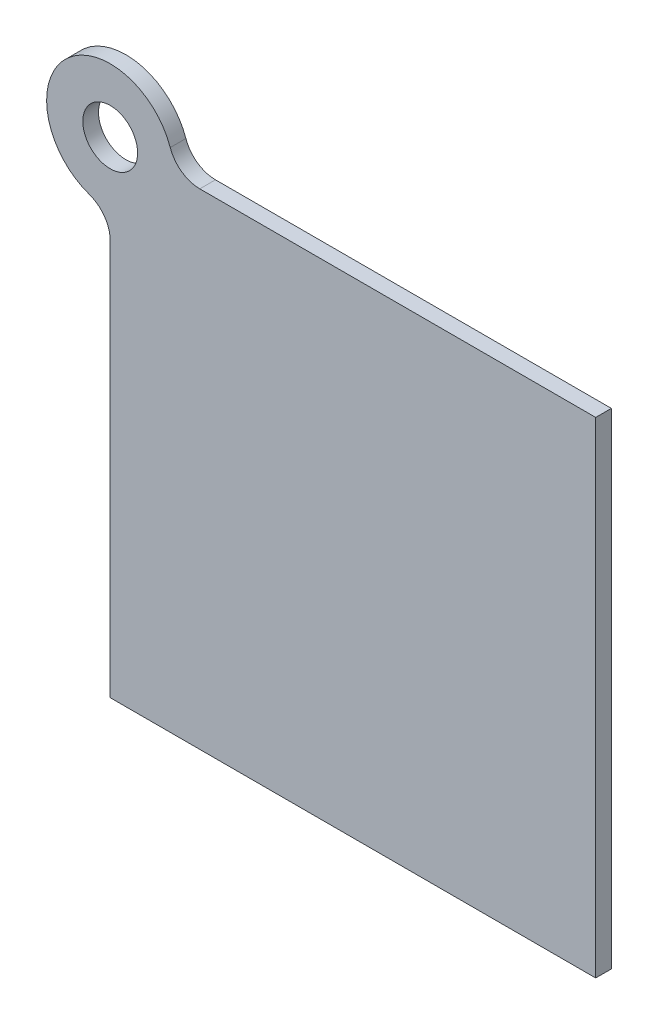
SolidWorks part; units mm, degrees
ref_plane "Front Plane" through (0, 0, 0) normal (0, 0, 1) x (1, 0, 0)
ref_plane "Top Plane" through (0, 0, 0) normal (0, 1, 0) x (1, 0, 0)
ref_plane "Right Plane" through (0, 0, 0) normal (1, 0, 0) x (0, 0, -1)
sketch "Sketch1" plane through (0, 0, 0) normal (0, 0, 1) x (1, 0, 0)
  line L0 (0, -10.3124) -> (0, -78.74)
  line L1 (0, -78.74) -> (78.74, -78.74)
  line L2 (78.74, -78.74) -> (78.74, 0)
  line L3 (78.74, 0) -> (10.3124, 0)
  circle A0 centre (0, 0) radius 4.445
  arc A1 (10.3124, 0) -> (0, -10.3124) centre (0, 0) ccw
  dimension "D1" = 8.89
  dimension "D2" = 10.3124
  dimension "D3" = 78.74
  dimension "D4" = 78.74
extrude "Boss-Extrude1" add sketch "Sketch1" along normal blind 2.54
fillet "Fillet1" radius 5.08 2 edges at (0, -10.3124, 1.27) (10.3124, 0, 1.27)
